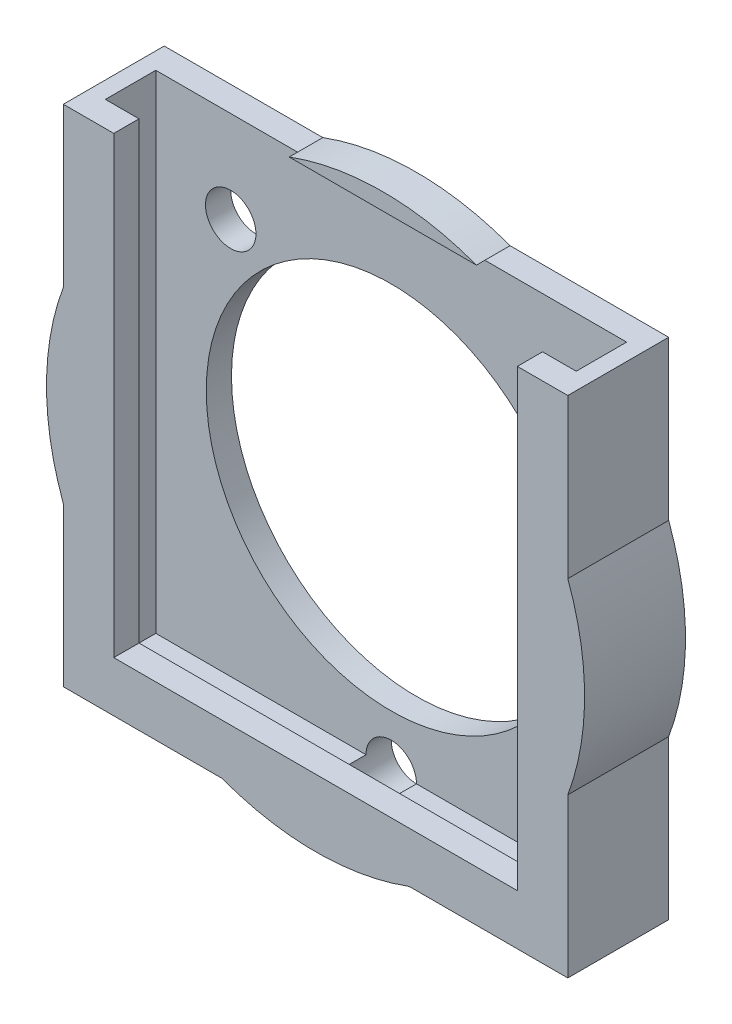
SolidWorks part; units mm, degrees
ref_plane "Front Plane" through (0, 0, 0) normal (0, 0, 1) x (1, 0, 0)
ref_plane "Top Plane" through (0, 0, 0) normal (0, 1, 0) x (1, 0, 0)
ref_plane "Right Plane" through (0, 0, 0) normal (1, 0, 0) x (0, 0, -1)
sketch "Sketch1" plane through (0, 0, 0) normal (0, 0, 1) x (1, 0, 0)
  line L0 (-15, -15) -> (-15, 15)
  line L1 (-15, -15) -> (15, -15)
  line L2 (-15, 15) -> (15, 15)
  line L3 (15, -15) -> (15, 15)
  line L4 (-15, -15) -> (15, 15) construction
  line L5 (-15, 15) -> (15, -15) construction
  circle A0 centre (0, 0) radius 15
  circle A1 centre (0, 0) radius 16
  circle A2 centre (0, 0) radius 11
  circle A3 centre (-9.5459, 9.5459) radius 1.5
  circle A4 centre (9.5459, 9.5459) radius 1.5
  circle A5 centre (0, -14) radius 1.5
extrude "Boss-Extrude1" add sketch "Sketch1" along normal blind 6 contours L2 A1 L0 A0 | L2 A1 | A1 L2 L0 | A1 L3 L2 | L3 A1 L2 A0 | A5 A0 A4 A3 A2 | A5 L1 A1 L3 A0 | L3 A1 | A1 L1 L3 | A5 L1 A1 | A5 A0 L0 A1 L1 | L0 A1
sketch "Sketch2" plane through (0, 0, 6) normal (0, 0, 1) x (1, 0, 0)
  circle A0 centre (0, 0) radius 11
extrude "Cut-Extrude1" cut sketch "Sketch2" against normal blind 10
sketch "Sketch3" plane through (0, 0, 6) normal (0, 0, 1) x (1, 0, 0)
  line L0 (-15, 15) -> (15, 15)
  line L1 (15, 15) -> (12, 15)
  line L2 (12, 15) -> (12, -12)
  line L3 (12, -12) -> (-12, -12)
  line L4 (-12, -12) -> (-12, 15)
  circle A0 centre (0, 0) radius 16
  circle M1 centre (0, 0) radius 11
  arc M5 (5.5678, 15) -> (-5.5678, 15) centre (0, 0) ccw
  line M6 (-5.5678, 15) -> (-15, 15)
extrude "Cut-Extrude2" cut sketch "Sketch3" against normal blind 4 contours L2 A0 L0 L4 L3 M1 | L0 M5 | A0 L4 M6 | A0 L2 L0 | A0 L3 L2 | A0 L4 L3
sketch "Sketch4" plane through (0, 15, 0) normal (0, 1, 0) x (1, 0, 0)
  line L0 (-12, -2) -> (-14, -2)
  line L1 (-14, -2) -> (-14, -4)
  line L2 (-14, -4) -> (14, -4)
  line L3 (14, -4) -> (14, -2)
  line L4 (14, -2) -> (12, -2)
  line L5 (-12, -2) -> (12, -2)
extrude "Cut-Extrude3" cut sketch "Sketch4" against normal blind 29 contours L5 L4 L3 L2 L1 L0
sketch "Sketch5" plane through (0, 15, 0) normal (0, 1, 0) x (1, 0, 0)
  line L0 (-14, -4) -> (14, -2)
  line L1 (-14, -4.5) -> (14, -4.5)
  line L2 (-14, -4.5) -> (-14, -1.5)
  line L3 (14, -4.5) -> (14, -1.5)
  line L4 (-14, -1.5) -> (14, -1.5)
  line L5 (-14, -4.5) -> (14, -1.5) construction
  line L6 (14, -4.5) -> (-14, -1.5) construction
  point P5 (0, -3)
  line M6 (-14, -4) -> (-14, -2)
  line M7 (-14, -2) -> (-5.5678, -2)
  line M8 (-5.5678, -2) -> (-5.5678, 0)
  line M12 (-12, -6) -> (-12, -4)
  line M13 (-12, -4) -> (-14, -4)
extrude "Cut-Extrude4" cut sketch "Sketch5" against normal blind 29 contours L4 L0 L3 M8 M7 M6 | L1 L3 L0 M13 M12 | L4 L2 M7 M8 | L2 L1 M12 M13
sketch "Sketch6" plane through (0, 0, 0) normal (0, 0, -1) x (-1, 0, 0)
  circle A0 centre (-9.5459, 9.5459) radius 1.5
  circle A1 centre (9.5459, 9.5459) radius 1.5
  circle A2 centre (0, -14) radius 1.5
extrude "Cut-Extrude5" cut sketch "Sketch6" against normal blind 3
